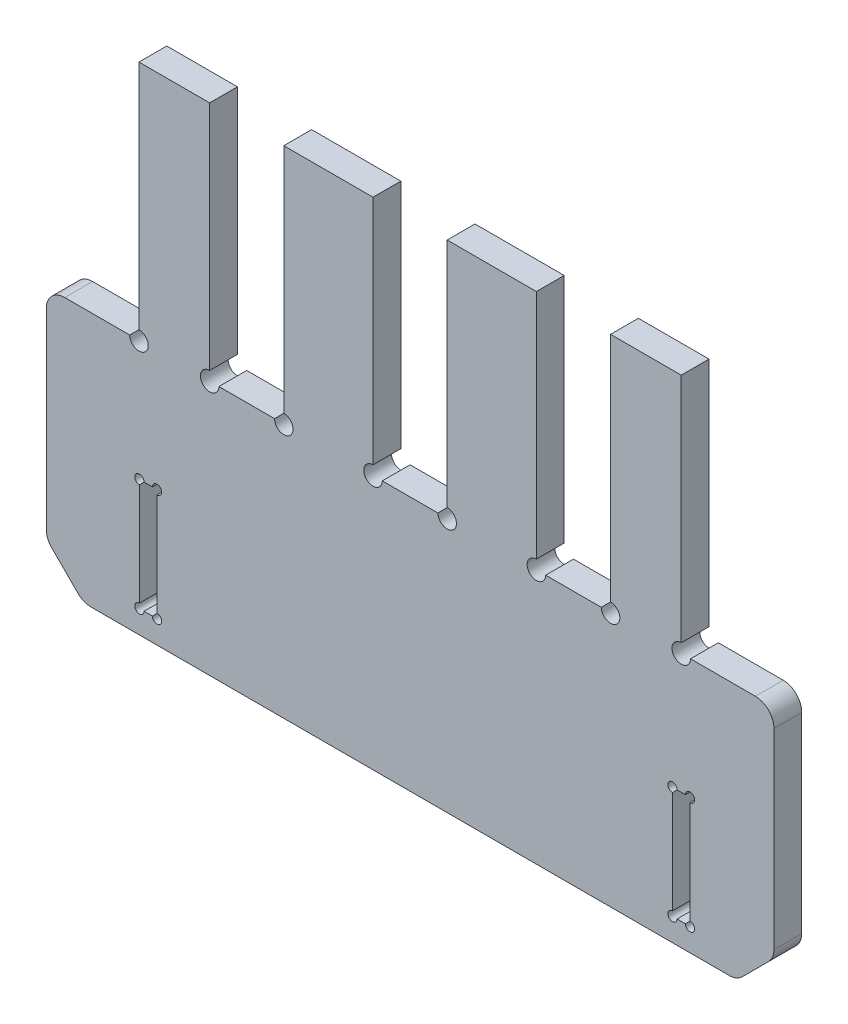
SolidWorks part; units mm, degrees
material "Thornel Mat VMA"
ref_plane "前视基准面" through (0, 0, 0) normal (0, 0, 1) x (1, 0, 0)
ref_plane "上视基准面" through (0, 0, 0) normal (0, 1, 0) x (1, 0, 0)
ref_plane "右视基准面" through (0, 0, 0) normal (1, 0, 0) x (0, 0, -1)
sketch "草图1" plane through (0, 0, 0) normal (0, 0, 1) x (1, 0, 0)
  line L1 (-39.25, -26.75) -> (39.25, -26.75)
  line L2 (-39.25, -26.75) -> (-39.25, 26.75)
  line L3 (-39.25, 26.75) -> (39.25, 26.75)
  line L4 (39.25, -26.75) -> (39.25, 26.75)
  line L5 (-39.25, -26.75) -> (39.25, 26.75) construction
  line L6 (-39.25, 26.75) -> (39.25, -26.75) construction
  point P0 (0, 0)
  dimension "D1" = 53.5
  dimension "D2" = 78.5
extrude "凸台-拉伸1" add sketch "草图1" along normal blind 3
sketch "草图2" plane through (0, 0, 0) normal (0, 0, -1) x (-1, 0, 0)
  line L1 (28.25, -24.25) -> (30.25, -24.25) construction
  line L2 (28.25, -24.25) -> (28.25, -12.25) construction
  line L3 (28.25, -12.25) -> (30.25, -12.25) construction
  line L4 (30.25, -24.25) -> (30.25, -12.25) construction
  line L9 (39.25, 26.75) -> (39.25, -26.75) construction
  line L10 (39.25, -26.75) -> (-39.25, -26.75) construction
  line L11 (0, -26.75) -> (0, 26.75) construction
  line L12 (-39.25, 26.75) -> (39.25, 26.75) construction
  line L13 (-30.25, -24.25) -> (-30.25, -12.25)
  line L14 (-28.25, -12.25) -> (-30.25, -12.25)
  line L15 (-28.25, -24.25) -> (-28.25, -12.25)
  line L16 (-28.25, -24.25) -> (-30.25, -24.25)
  dimension "D2" = 9
  dimension "D4" = 2.5
  dimension "D6" = 12
  dimension "D8" = 2
extrude "切除-拉伸1" cut sketch "草图2" against normal blind 5
sketch "草图3" plane through (0, 0, 0) normal (0, 0, -1) x (-1, 0, 0)
  line L0 (-13.625, 0.25) -> (-13.625, 26.75)
  line L5 (-21.625, 0.25) -> (-13.625, 0.25)
  line L6 (-21.625, 26.75) -> (-21.625, 0.25)
  line L7 (-13.625, 26.75) -> (-21.625, 26.75)
  line L12 (39.25, 0.25) -> (31.25, 0.25)
  line L25 (39.25, 26.75) -> (39.25, -26.75) construction
  line L26 (31.25, 0.25) -> (31.25, 26.75)
  line L27 (-39.25, 26.75) -> (39.25, 26.75) construction
  line L28 (31.25, 26.75) -> (39.25, 26.75)
  line L29 (39.25, 26.75) -> (39.25, 0.25)
  line L30 (39.25, -26.75) -> (-39.25, -26.75) construction
  line L31 (21.625, 26.75) -> (21.625, 0.25)
  line L32 (21.625, 0.25) -> (13.625, 0.25)
  line L33 (13.625, 0.25) -> (13.625, 26.75)
  line L34 (13.625, 26.75) -> (21.625, 26.75)
  line L35 (0, 0) -> (0, -26.75) construction
  line L36 (-4, 26.75) -> (4, 26.75)
  line L37 (4, 26.75) -> (4, 0.25)
  line L38 (4, 0.25) -> (-4, 0.25)
  line L39 (-4, 0.25) -> (-4, 26.75)
  line L40 (17.625, 0.25) -> (17.625, 26.75) construction
  line L41 (35.25, 0.25) -> (35.25, 26.75) construction
  line L42 (-31.25, 26.75) -> (-39.25, 26.75)
  line L43 (-31.25, 0.25) -> (-31.25, 26.75)
  line L44 (-39.25, 0.25) -> (-31.25, 0.25)
  line L45 (-39.25, 26.75) -> (-39.25, 0.25)
  point P25 (0, 0.25)
  dimension "D1" = 27
  dimension "D2" = 8
  dimension "D4" = 8
  dimension "D5" = 2
  dimension "D6" = 4
extrude "切除-拉伸2" cut sketch "草图3" against normal through all
sketch "草图6" plane through (0, 0, 0) normal (0, 0, -1) x (-1, 0, 0)
  line L0 (0, 7.589) -> (0, -30.5527) construction
  circle A2 centre (12.3496, -9.7954) radius 3.2976
sketch "草图7" plane through (0, 0, 0) normal (0, 0, -1) x (-1, 0, 0)
  line L0 (31.25, 0.25) -> (29.25, 0.25)
  line L1 (29.25, 0.25) -> (29.25, 26.75)
  line L2 (21.625, 26.75) -> (31.25, 26.75) construction
  line L3 (29.25, 26.75) -> (31.25, 26.75)
  line L4 (31.25, 26.75) -> (31.25, 0.25)
  line L5 (0, -26.75) -> (0, 0) construction
  line L6 (39.25, -26.75) -> (-39.25, -26.75) construction
  line L7 (-31.25, 26.75) -> (-31.25, 0.25)
  line L8 (-29.25, 26.75) -> (-31.25, 26.75)
  line L9 (-29.25, 0.25) -> (-29.25, 26.75)
  line L10 (-31.25, 0.25) -> (-29.25, 0.25)
  dimension "D1" = 2
extrude "切除-拉伸3" cut sketch "草图7" against normal blind 10
sketch "草图8" plane through (0, 0, 0) normal (0, 0, -1) x (-1, 0, 0)
  line L0 (29.25, 6.875) -> (29.25, -36.0421) construction
  line L2 (39.25, 0.25) -> (39.25, -26.75) construction
  line L3 (-28.25, -18.25) -> (46.788, -18.25) construction
  line L4 (-28.25, -24.25) -> (-28.25, -12.25) construction
  line L6 (27.25, -24.25) -> (29.25, -24.25)
  line L7 (27.25, -24.25) -> (27.25, -12.25)
  line L8 (27.25, -12.25) -> (29.25, -12.25)
  line L9 (29.25, -24.25) -> (29.25, -12.25)
  line L10 (27.25, -24.25) -> (29.25, -12.25) construction
  line L11 (27.25, -12.25) -> (29.25, -24.25) construction
  point P8 (28.25, -18.25)
  dimension "D1" = 10
  dimension "D2" = 2
  dimension "D3" = 12
extrude "切除-拉伸4" cut sketch "草图8" against normal blind 10
sketch "草图9" plane through (0, 0, 0) normal (0, 0, -1) x (-1, 0, 0)
  line L0 (27.25, -24.25) -> (29.25, -24.25) construction
  line L1 (29.25, -24.25) -> (29.25, -12.25) construction
  line L2 (29.25, -12.25) -> (27.25, -12.25) construction
  line L3 (27.25, -12.25) -> (27.25, -24.25) construction
  line L4 (-30.25, -24.25) -> (-28.25, -24.25) construction
  line L5 (-28.25, -24.25) -> (-28.25, -12.25) construction
  line L6 (-28.25, -12.25) -> (-30.25, -12.25) construction
  line L7 (-30.25, -12.25) -> (-30.25, -24.25) construction
  line L8 (27.25, -24.25) -> (29.25, -24.25)
  line L9 (29.25, -24.25) -> (29.25, -12.25)
  line L10 (29.25, -12.25) -> (27.25, -12.25)
  line L11 (27.25, -12.25) -> (27.25, -24.25)
  line L12 (-30.25, -24.25) -> (-28.25, -24.25)
  line L13 (-28.25, -24.25) -> (-28.25, -12.25)
  line L14 (-28.25, -12.25) -> (-30.25, -12.25)
  line L15 (-30.25, -12.25) -> (-30.25, -24.25)
  line L16 (27.22, -24.28) -> (29.28, -24.28)
  line L17 (29.28, -24.28) -> (29.28, -12.22)
  line L18 (29.28, -12.22) -> (27.22, -12.22)
  line L19 (27.22, -12.22) -> (27.22, -24.28)
  line L20 (-30.28, -24.28) -> (-28.22, -24.28)
  line L21 (-28.22, -24.28) -> (-28.22, -12.22)
  line L22 (-28.22, -12.22) -> (-30.28, -12.22)
  line L23 (-30.28, -12.22) -> (-30.28, -24.28)
  dimension "D1" = 0.03
extrude "切除-拉伸5" cut sketch "草图9" against normal blind 10
chamfer "倒角1" distance 4 angle 45 2 edges at (-39.25, -26.75, 1.5) (39.25, -26.75, 1.5)
sketch "草图11" plane through (0, 0.25, 0) normal (0, 1, 0) x (1, 0, 0)
  line L0 (-39.25, 0) -> (-39.25, -3)
  line L1 (-39.25, -3) -> (39.25, -3)
  line L2 (39.25, -3) -> (39.25, 0)
  line L3 (39.25, 0) -> (-39.25, 0)
extrude "凸台-拉伸2" add sketch "草图11" along normal blind 0.5
fillet "圆角2" radius 2 6 edges at (39.25, -22.75, 1.5) (35.25, -26.75, 1.5) (-35.25, -26.75, 1.5) (-39.25, -22.75, 1.5) (-39.25, 0.75, 1.5) (39.25, 0.75, 1.5)
sketch "草图14" plane through (0, 0, 0) normal (0, 0, -1) x (-1, 0, 0)
  line L0 (-30.28, -24.28) -> (-28.22, -24.28) construction
  line L1 (-30.28, -12.22) -> (-30.2, -12.22)
  line L2 (-30.28, -12.22) -> (-30.28, -24.28)
  line L3 (-30.28, -24.28) -> (-30.2, -24.28)
  line L4 (-30.2, -12.22) -> (-30.2, -24.28)
  line L7 (-28.22, -12.22) -> (-28.3, -12.22)
  line L8 (-28.22, -12.22) -> (-28.22, -24.28)
  line L9 (-28.22, -24.28) -> (-28.3, -24.28)
  line L10 (-28.3, -12.22) -> (-28.3, -24.28)
  dimension "D1" = 0.08
  dimension "D2" = 0.08
extrude "凸台-拉伸3" add sketch "草图14" against normal up to surface (3 mm away) up to face at (0, 0.8246, 3)
sketch "草图15" plane through (0, 0, 0) normal (0, 0, -1) x (-1, 0, 0)
  line L0 (27.22, -24.28) -> (29.28, -24.28) construction
  line L1 (27.22, -12.22) -> (27.3, -12.22)
  line L2 (27.22, -12.22) -> (27.22, -24.28)
  line L3 (27.22, -24.28) -> (27.3, -24.28)
  line L4 (27.3, -12.22) -> (27.3, -24.28)
  line L6 (29.28, -12.22) -> (29.2, -12.22)
  line L7 (29.28, -12.22) -> (29.28, -24.28)
  line L8 (29.28, -24.28) -> (29.2, -24.28)
  line L9 (29.2, -12.22) -> (29.2, -24.28)
  dimension "D1" = 0.08
  dimension "D2" = 0.08
extrude "凸台-拉伸4" add sketch "草图15" against normal up to surface (3 mm away) up to face at (29.25, -18.25, 3)
sketch "草图16" plane through (0, 0, 0) normal (0, 0, -1) x (-1, 0, 0)
  circle A0 centre (-30.2, -12.22) radius 0.5
  circle A1 centre (-28.3, -12.22) radius 0.5
  circle A2 centre (-30.2, -24.28) radius 0.5
  circle A3 centre (-28.3, -24.28) radius 0.5
  circle A4 centre (27.3, -12.22) radius 0.5
  circle A5 centre (29.2, -12.22) radius 0.5
  circle A6 centre (27.3, -24.28) radius 0.5
  circle A7 centre (29.2, -24.28) radius 0.5
extrude "切除-拉伸6" cut sketch "草图16" against normal blind 10
sketch "草图17" plane through (0, 0, 0) normal (0, 0, -1) x (-1, 0, 0)
  circle A0 centre (-29.25, 0.75) radius 1
  circle A1 centre (-21.625, 0.75) radius 1
  circle A2 centre (-13.625, 0.75) radius 1
  circle A3 centre (-4, 0.75) radius 1
  circle A4 centre (4, 0.75) radius 1
  circle A5 centre (13.625, 0.75) radius 1
  circle A6 centre (21.625, 0.75) radius 1
  circle A7 centre (29.25, 0.75) radius 1
  dimension "D1" = 2
  dimension "D2" = 2
extrude "切除-拉伸7" cut sketch "草图17" against normal blind 10
